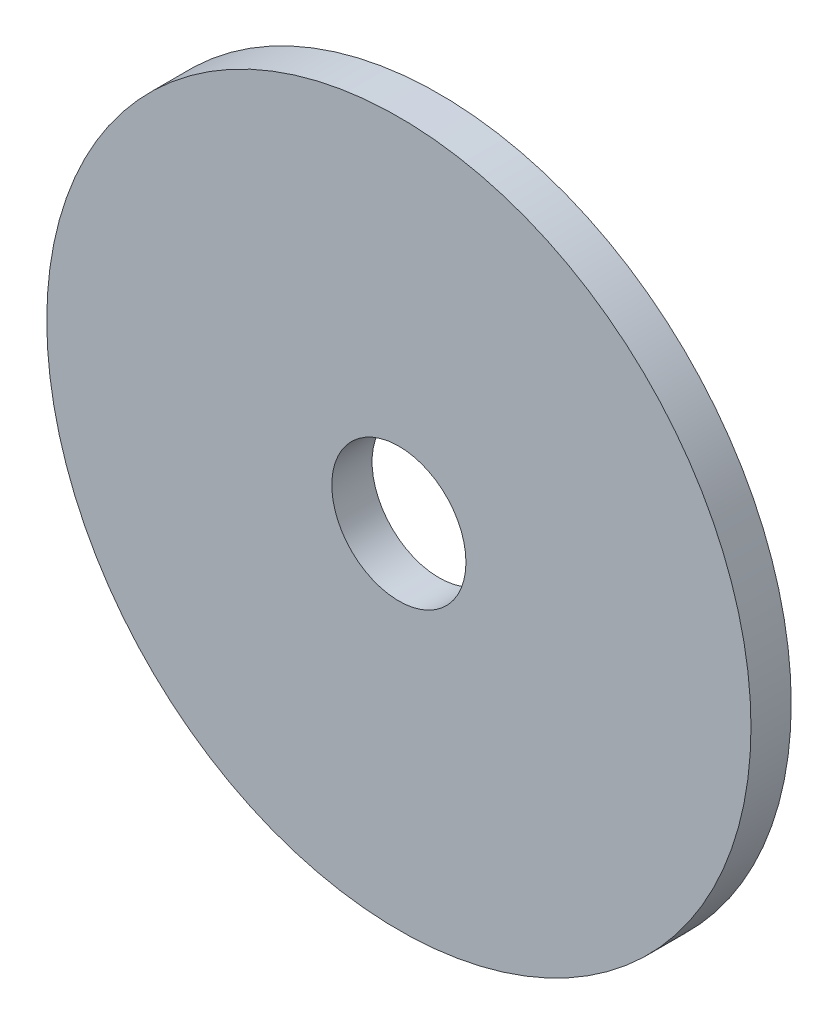
SolidWorks part; units mm, degrees
ref_plane "Plan de face" through (0, 0, 0) normal (0, 0, 1) x (1, 0, 0)
ref_plane "Plan de dessus" through (0, 0, 0) normal (0, 1, 0) x (1, 0, 0)
ref_plane "Plan de droite" through (0, 0, 0) normal (1, 0, 0) x (0, 0, -1)
sketch "Esquisse1" plane through (0, 0, 0) normal (0, 0, 1) x (1, 0, 0)
  circle A0 centre (0, 0) radius 10
  circle A1 centre (0, 0) radius 52.5
  dimension "D1" = 20
  dimension "D2" = 105
extrude "Boss.-Extru.1" add sketch "Esquisse1" along normal blind 6
